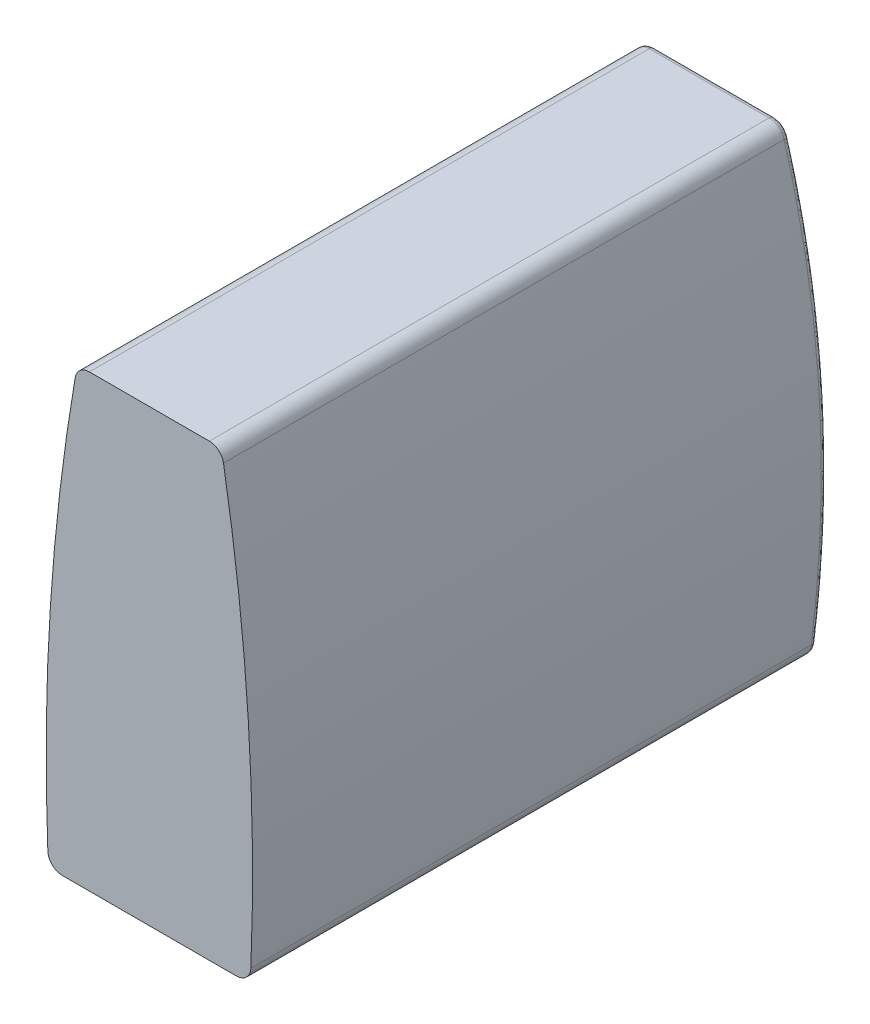
SolidWorks part; units mm, degrees
ref_plane "Front Plane" through (0, 0, 0) normal (0, 0, 1) x (1, 0, 0)
ref_plane "Top Plane" through (0, 0, 0) normal (0, 1, 0) x (1, 0, 0)
ref_plane "Right Plane" through (0, 0, 0) normal (1, 0, 0) x (0, 0, -1)
sketch "Sketch1" plane through (0, 0, 0) normal (0, 0, 1) x (1, 0, 0)
  line L0 (-1.0399, 3.9) -> (1.0399, 3.9)
  line L2 (1.5109, -3.9) -> (-1.5109, -3.9)
  line L4 (0, -55) -> (0, 55) construction
  line L5 (55, 0) -> (-55, 0) construction
  arc A0 (-1.2863, 3.6923) -> (-1.7607, -3.6603) centre (33.2099, -2.225) ccw
  arc A1 (1.2863, 3.6923) -> (1.7607, -3.6603) centre (-33.2099, -2.225) cw
  arc A2 (1.7607, -3.6603) -> (1.5109, -3.9) centre (1.5109, -3.65) cw
  arc A3 (-1.5109, -3.9) -> (-1.7607, -3.6603) centre (-1.5109, -3.65) cw
  arc A4 (1.0399, 3.9) -> (1.2863, 3.6923) centre (1.0399, 3.65) cw
  arc A5 (-1.0399, 3.9) -> (-1.2863, 3.6923) centre (-1.0399, 3.65) ccw
  point P12 (1.75, -3.9)
  point P15 (-1.75, -3.9)
  point P18 (1.25, 3.9)
  point P21 (-1.25, 3.9)
  dimension "D7" = 35
  dimension "D8" = 35
  dimension "D9" = 0.25
  dimension "D1" = 3.5
  dimension "D2" = 1.75
  dimension "D3" = 2.5
  dimension "D4" = 1.25
  dimension "D5" = 7.8
  dimension "D6" = 3.9
extrude "Boss-Extrude1" add sketch "Sketch1" along normal blind 10
sketch "Sketch2" plane through (0, 0, 0) normal (1, 0, 0) x (0, 0, -1)
  line L0 (-10, 3.9) -> (0, 3.9) construction
  line L1 (-10, -3.9) -> (0, -3.9) construction
  line L2 (0, 1.9691) -> (0, -1.9691) construction
  line L3 (-0.2, 3.9) -> (0.7266, 4.7109)
  line L4 (0.7266, 4.7109) -> (3.4349, -0.7058)
  line L5 (3.4349, -0.7058) -> (0.497, -4.8257)
  line L6 (0.497, -4.8257) -> (-0.2, -3.9)
  arc A0 (-0.2, 3.9) -> (-0.2, -3.9) centre (-38.125, 0) cw
  dimension "D1" = 0.2
  dimension "D2" = 0.2
extrude "Cut-Extrude1" cut sketch "Sketch2" against normal mid plane 10
fillet "Fillet1" radius 0.1 8 edges at (1.6664, -3.8457, 0.1945) (1.2054, 3.8373, 0.1936) (0, 3.9, 0.2) (-1.1954, 3.8457, 0.1945) (-1.6991, -3.8146, 0.1913) (0, -3.9, 0.2)
sketch "Sketch3" plane through (0, 0, 10) normal (0, 0, 1) x (1, 0, 0)
  line L2 (1.0399, 3.9) -> (-1.0399, 3.9)
  line L3 (-1.5109, -3.9) -> (1.5109, -3.9)
  line L4 (1.0399, 3.9) -> (-1.0399, 3.9)
  line L5 (-1.5109, -3.9) -> (1.5109, -3.9)
  arc A6 (1.5109, -3.9) -> (1.7607, -3.6603) centre (1.5109, -3.65) ccw
  arc A7 (1.7607, -3.6603) -> (1.2863, 3.6923) centre (-33.2099, -2.225) ccw
  arc A8 (1.2863, 3.6923) -> (1.0399, 3.9) centre (1.0399, 3.65) ccw
  arc A9 (-1.0399, 3.9) -> (-1.2863, 3.6923) centre (-1.0399, 3.65) ccw
  arc A10 (-1.2863, 3.6923) -> (-1.7607, -3.6603) centre (33.2099, -2.225) ccw
  arc A11 (-1.7607, -3.6603) -> (-1.5109, -3.9) centre (-1.5109, -3.65) ccw
  arc A12 (1.5109, -3.9) -> (1.7607, -3.6603) centre (1.5109, -3.65) ccw
  arc A13 (1.7607, -3.6603) -> (1.2863, 3.6923) centre (-33.2099, -2.225) ccw
  arc A14 (1.2863, 3.6923) -> (1.0399, 3.9) centre (1.0399, 3.65) ccw
  arc A15 (-1.0399, 3.9) -> (-1.2863, 3.6923) centre (-1.0399, 3.65) ccw
  arc A16 (-1.2863, 3.6923) -> (-1.7607, -3.6603) centre (33.2099, -2.225) ccw
  arc A17 (-1.7607, -3.6603) -> (-1.5109, -3.9) centre (-1.5109, -3.65) ccw
  dimension "D1" = 0
